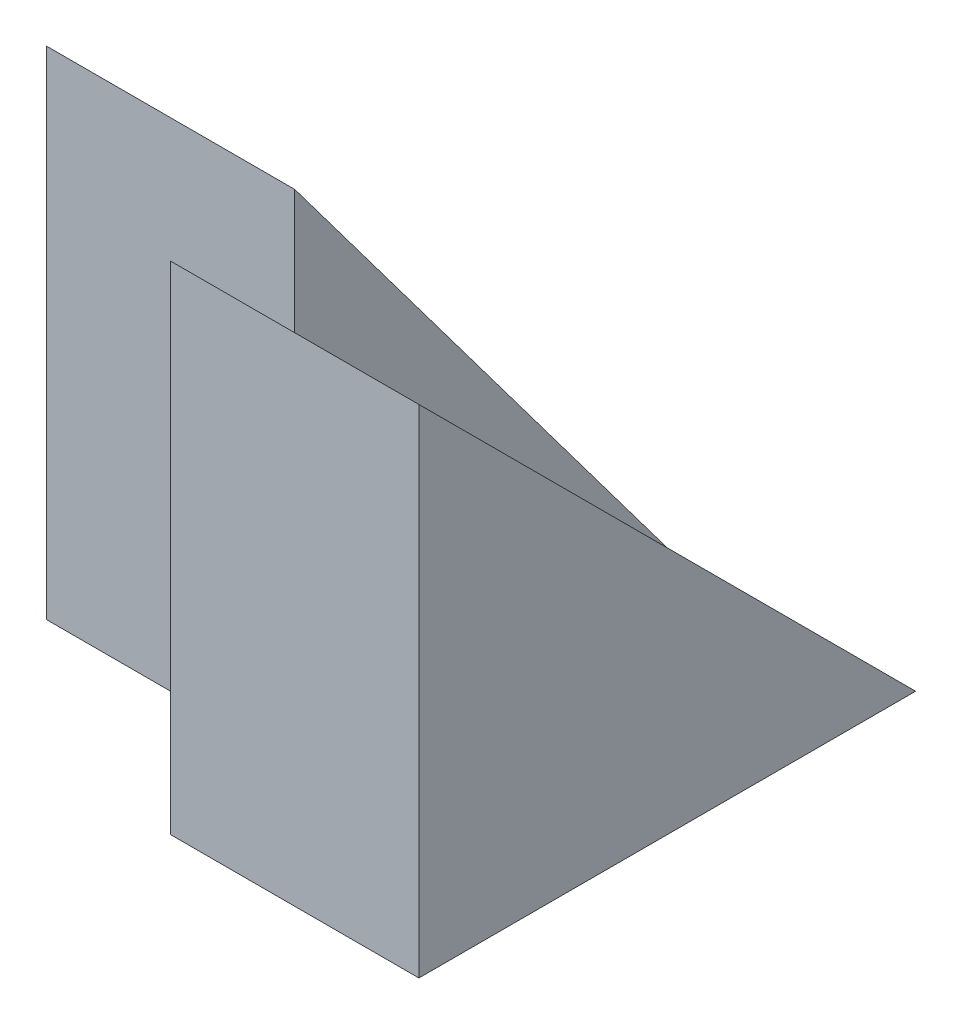
SolidWorks part; units mm, degrees
ref_plane "Front Plane" through (0, 0, 0) normal (0, 0, 1) x (1, 0, 0)
ref_plane "Top Plane" through (0, 0, 0) normal (0, 1, 0) x (1, 0, 0)
ref_plane "Right Plane" through (0, 0, 0) normal (1, 0, 0) x (0, 0, -1)
sketch "Sketch1" plane through (0, 0, 0) normal (1, 0, 0) x (0, 0, -1)
  line L1 (0, 0) -> (4, 0)
  line L2 (0, 0) -> (0, 4)
  line L3 (0, 4) -> (4, 4)
  line L4 (4, 0) -> (4, 4)
  dimension "D1" = 4
  dimension "D2" = 4
extrude "Boss-Extrude1" add sketch "Sketch1" along normal blind 2
sketch "Sketch2" plane through (0, 0, 0) normal (-1, 0, 0) x (0, 0, 1)
  line L0 (-1, 0) -> (-1, 4)
  line L1 (0, 0) -> (-4, 0) construction
  line L2 (-4, 0) -> (-4, 4) construction
  line L3 (-4, 4) -> (-4, 0)
  line L4 (-4, 0) -> (-1, 0)
  line L5 (-4, 4) -> (0, 4) construction
  line L6 (-1, 4) -> (-4, 4)
  dimension "D1" = 3
  dimension "D2" = 4
extrude "Boss-Extrude2" add sketch "Sketch2" along normal blind 2
sketch "Sketch3" plane through (-2, 0, 0) normal (-1, 0, 0) x (0, 0, 1)
  line L0 (-1, 4) -> (-4, 0)
  line L1 (-4, 0) -> (-4, 4)
  line L2 (-4, 4) -> (-1, 4)
extrude "Cut-Extrude1" cut sketch "Sketch3" against normal blind 2
sketch "Sketch4" plane through (2, 0, 0) normal (1, 0, 0) x (0, 0, -1)
  line L0 (4, 0) -> (0, 4)
  line L1 (0, 4) -> (4, 4)
  line L2 (4, 4) -> (4, 0)
extrude "Cut-Extrude2" cut sketch "Sketch4" against normal blind 2
